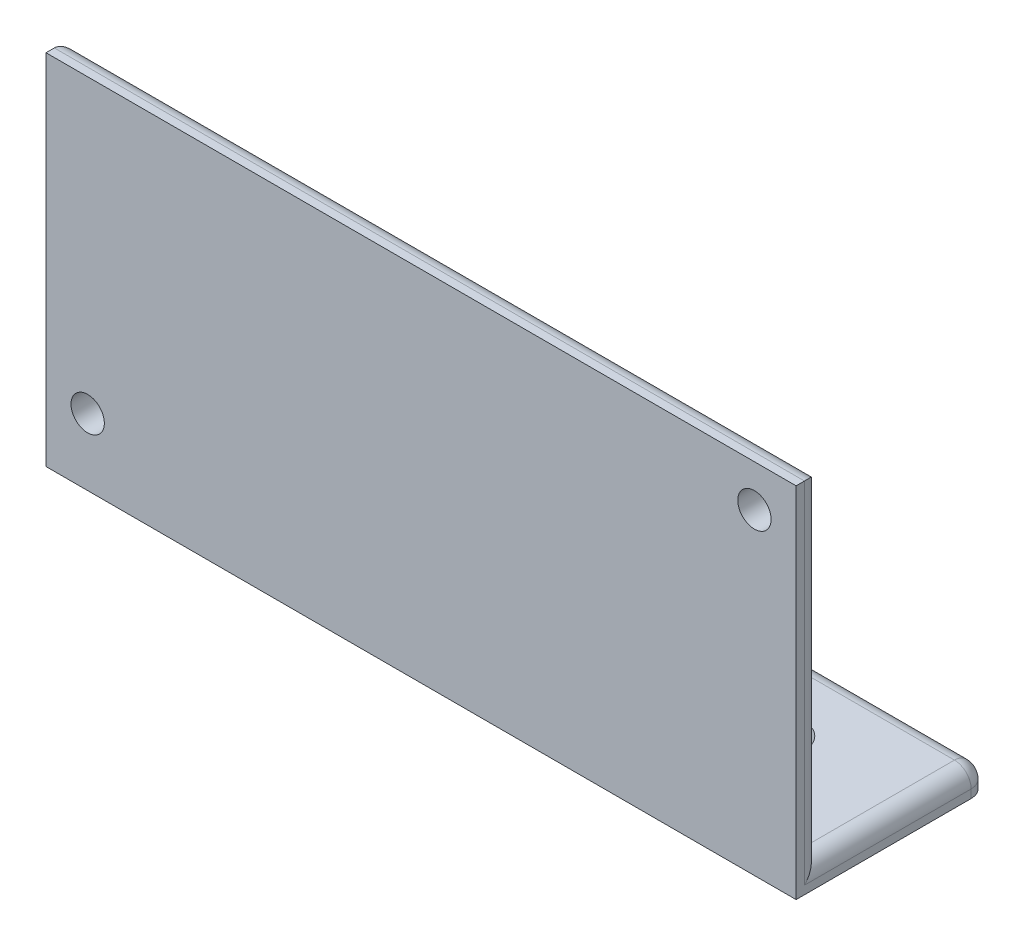
SolidWorks part; units mm, degrees
ref_plane "Front Plane" through (0, 0, 0) normal (0, 0, 1) x (1, 0, 0)
ref_plane "Top Plane" through (0, 0, 0) normal (0, 1, 0) x (1, 0, 0)
ref_plane "Right Plane" through (0, 0, 0) normal (1, 0, 0) x (0, 0, -1)
sketch "Sketch1" plane through (0, 0, 0) normal (0, 0, 1) x (1, 0, 0)
  line L1 (-22.5, 10) -> (22.5, 10)
  line L2 (-22.5, 10) -> (-22.5, -10)
  line L3 (-22.5, -10) -> (22.5, -10)
  line L4 (22.5, 10) -> (22.5, -10)
  circle A0 centre (20, 7.5) radius 1
  circle A1 centre (-20, -7.5) radius 1
  point P11 (0, 0)
  dimension "D1" = 2
extrude "Boss-Extrude1" add sketch "Sketch1" along normal blind 1.5
sketch "Sketch2" plane through (0, -10, 0) normal (0, -1, 0) x (1, 0, 0)
  line L0 (0, -0.825) -> (0, 0.825) construction
  line L1 (22.5, 1.5) -> (-22.5, 1.5)
  line L2 (22.5, 1.5) -> (22.5, -10)
  line L3 (22.5, -10) -> (-22.5, -10)
  line L4 (-22.5, 1.5) -> (-22.5, -10)
  circle A0 centre (-15, -5) radius 1.5
  circle A1 centre (15, -5) radius 1.5
extrude "Boss-Extrude2" add sketch "Sketch2" along normal blind 1.5
fillet "Fillet1" radius 1 8 edges at (-22.5, -10.75, -10) (22.5, -10.75, -10) (0, -10, -10) (22.5, -10, -5) (-22.5, -10, -5) (-22.5, 0, 0) (22.5, 0, 0) (0, 10, 0)
